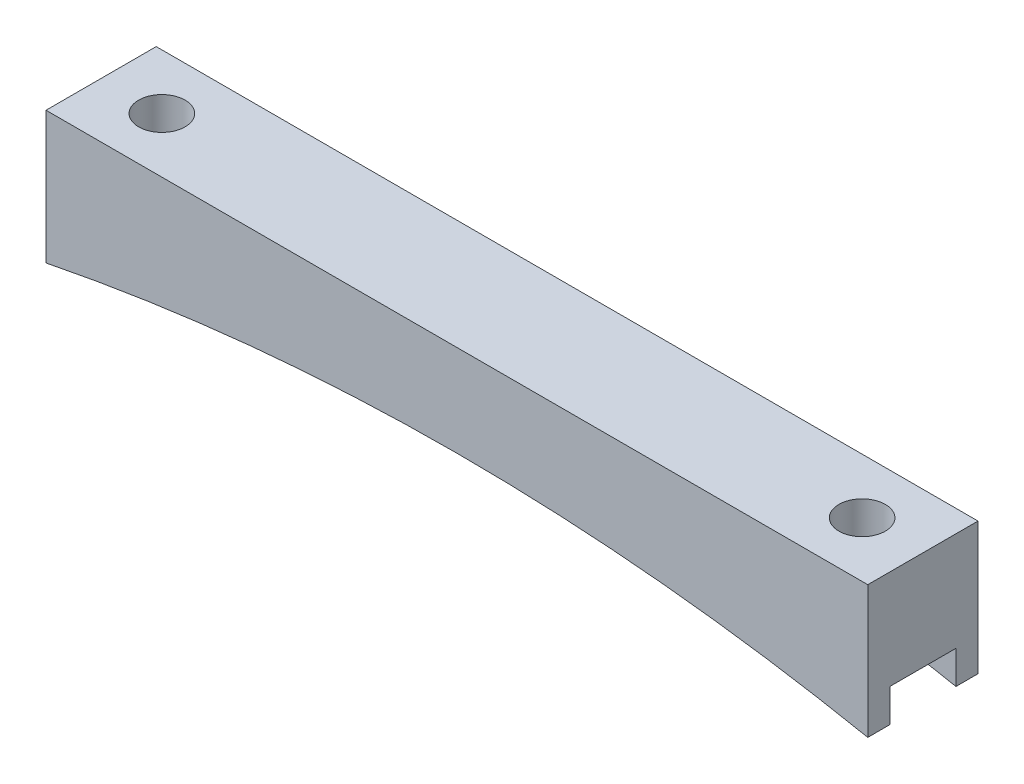
SolidWorks part; units mm, degrees
ref_plane "Front Plane" through (0, 0, 0) normal (0, 0, 1) x (1, 0, 0)
ref_plane "Top Plane" through (0, 0, 0) normal (0, 1, 0) x (1, 0, 0)
ref_plane "Right Plane" through (0, 0, 0) normal (1, 0, 0) x (0, 0, -1)
sketch "Sketch1" plane through (0, 0, 0) normal (0, 0, 1) x (1, 0, 0)
  line L0 (-47.34, 0) -> (47.34, 0)
  line L1 (-40.34, -2.54) -> (40.34, -2.54) construction
  line L2 (0, 0) -> (0, -4.6068) construction
  line L3 (47.34, 0) -> (47.34, -15.24)
  line L4 (-47.34, 0) -> (-47.34, -15.24)
  arc A0 (-47.34, -15.24) -> (47.34, -15.24) centre (0, -251.8507) cw
  point P4 (0, 0)
  point P9 (0, -2.54)
  dimension "D4" = 241.3
  dimension "D1" = 80.68
  dimension "D2" = 2.54
  dimension "D3" = 7
  dimension "D5" = 15.24
extrude "Boss-Extrude1" add sketch "Sketch1" along normal blind 12.7
sketch "Sketch2" plane through (0, 0, 0) normal (0, 1, 0) x (1, 0, 0)
  line L1 (-40.34, 0) -> (-40.34, -12.7) construction
  line L2 (-47.34, 0) -> (47.34, 0) construction
  line L3 (47.34, -12.7) -> (-47.34, -12.7) construction
  line L4 (40.34, 0) -> (40.34, -12.7) construction
  circle A0 centre (-40.34, -6.35) radius 2.675
  circle A1 centre (40.34, -6.35) radius 2.675
  circle A2 centre (-40.34, -6.35) radius 3 construction
  point P7 (-40.34, -6.35)
  dimension "D1" = 5.35
  dimension "D2" = 6
extrude "Cut-Extrude1" cut sketch "Sketch2" against normal through all
sketch "Sketch3" plane through (47.34, 0, 0) normal (1, 0, 0) x (0, 0, -1)
  line L0 (-12.7, -15.24) -> (0, -15.24) construction
  line L1 (-10.16, -15.24) -> (-2.54, -15.24)
  line L2 (-10.16, -15.24) -> (-10.16, -11.43)
  line L3 (-10.16, -11.43) -> (-2.54, -11.43)
  line L4 (-2.54, -15.24) -> (-2.54, -11.43)
  line L5 (-12.7, -15.24) -> (-12.7, 0) construction
  line L6 (0, -15.24) -> (0, 0) construction
  dimension "D1" = 2.54
  dimension "D2" = 2.54
  dimension "D3" = 3.81
extrude "Cut-Extrude2" cut sketch "Sketch3" against normal through all
